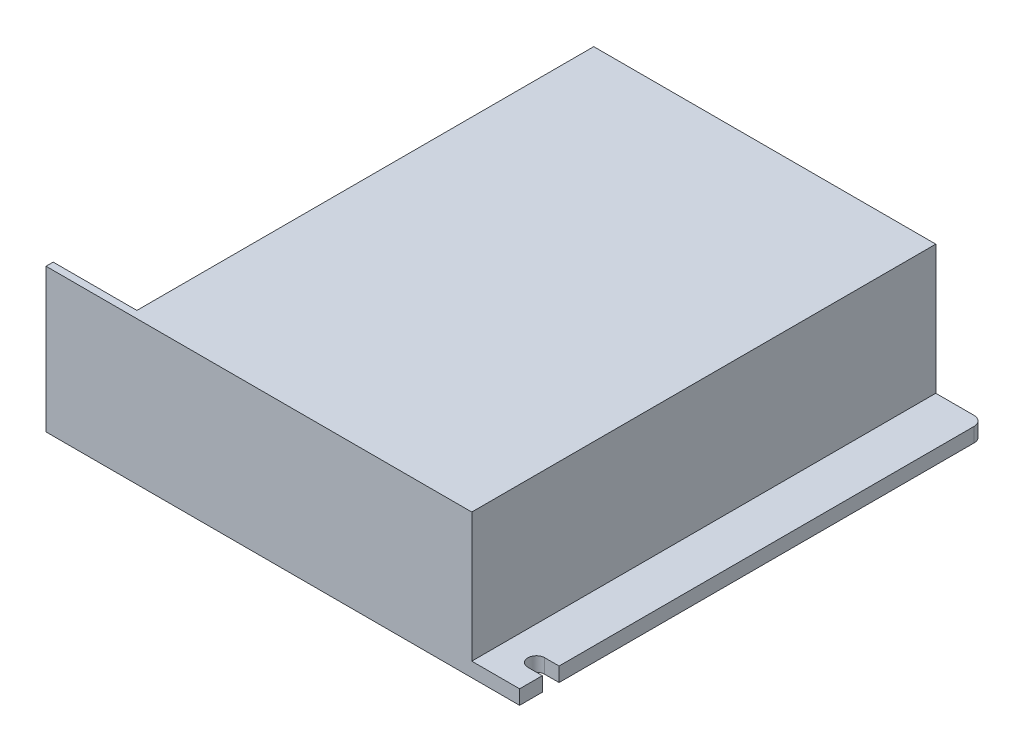
SolidWorks part; units mm, degrees
ref_plane "Front Plane" through (0, 0, 0) normal (0, 0, 1) x (1, 0, 0)
ref_plane "Top Plane" through (0, 0, 0) normal (0, 1, 0) x (1, 0, 0)
ref_plane "Right Plane" through (0, 0, 0) normal (1, 0, 0) x (0, 0, -1)
sketch "Sketch2" plane through (0, 0, 0) normal (0, 1, 0) x (1, 0, 0)
  line L1 (0, 0) -> (99, 0)
  line L2 (0, 0) -> (0, 97)
  line L3 (0, 97) -> (99, 97)
  line L4 (99, 0) -> (99, 97)
  dimension "D1" = 99
  dimension "D2" = 97
extrude "Boss-Extrude1" add sketch "Sketch2" along normal blind 3
sketch "Sketch4" plane through (0, 3, 0) normal (0, 1, 0) x (1, 0, 0)
  line L0 (99, 97) -> (0, 97) construction
  line L1 (17.5, 97) -> (89, 97)
  line L3 (17.5, 0) -> (89, 0)
  line L4 (89, 97) -> (89, 0)
  line L5 (0, 0) -> (99, 0) construction
  line L7 (99, 0) -> (99, 97) construction
  line L8 (17.5, 97) -> (17.5, 1.5)
  line L9 (17.5, 1.5) -> (0, 1.5)
  line L10 (0, 97) -> (0, 0) construction
  line L11 (0, 1.5) -> (0, 0)
  line L12 (0, 0) -> (17.5, 0)
  dimension "D1" = 17.5
  dimension "D2" = 10
  dimension "D3" = 1.5
extrude "Boss-Extrude2" add sketch "Sketch4" along normal blind 27
sketch "Sketch5" plane through (0, 3, 0) normal (0, 1, 0) x (1, 0, 0)
  line L0 (0, 97) -> (0, 1.5) construction
  line L1 (89, 0) -> (99, 0) construction
  line L2 (96, 8.25) -> (99, 8.25)
  line L3 (99, 0) -> (99, 97) construction
  line L4 (99, 8.25) -> (99, 4.75)
  line L5 (99, 4.75) -> (96, 4.75)
  circle A0 centre (3.5, 91.5) radius 1.75
  arc A1 (96, 4.75) -> (96, 8.25) centre (96, 6.5) cw
  point P0 (3.5, 91.5)
  point P1 (96, 6.5)
  point P14 (0, 0)
  point P16 (96, 3)
  point P17 (96, 10)
  dimension "D5" = 3.5
  dimension "D6" = 3.5
  dimension "D1" = 3.5
  dimension "D2" = 92.5
  dimension "D3" = 6.5
  dimension "D4" = 85
extrude "Cut-Extrude1" cut sketch "Sketch5" against normal through all
fillet "Fillet1" radius 2 2 edges at (0, 1.5, -97) (99, 1.5, -97)
